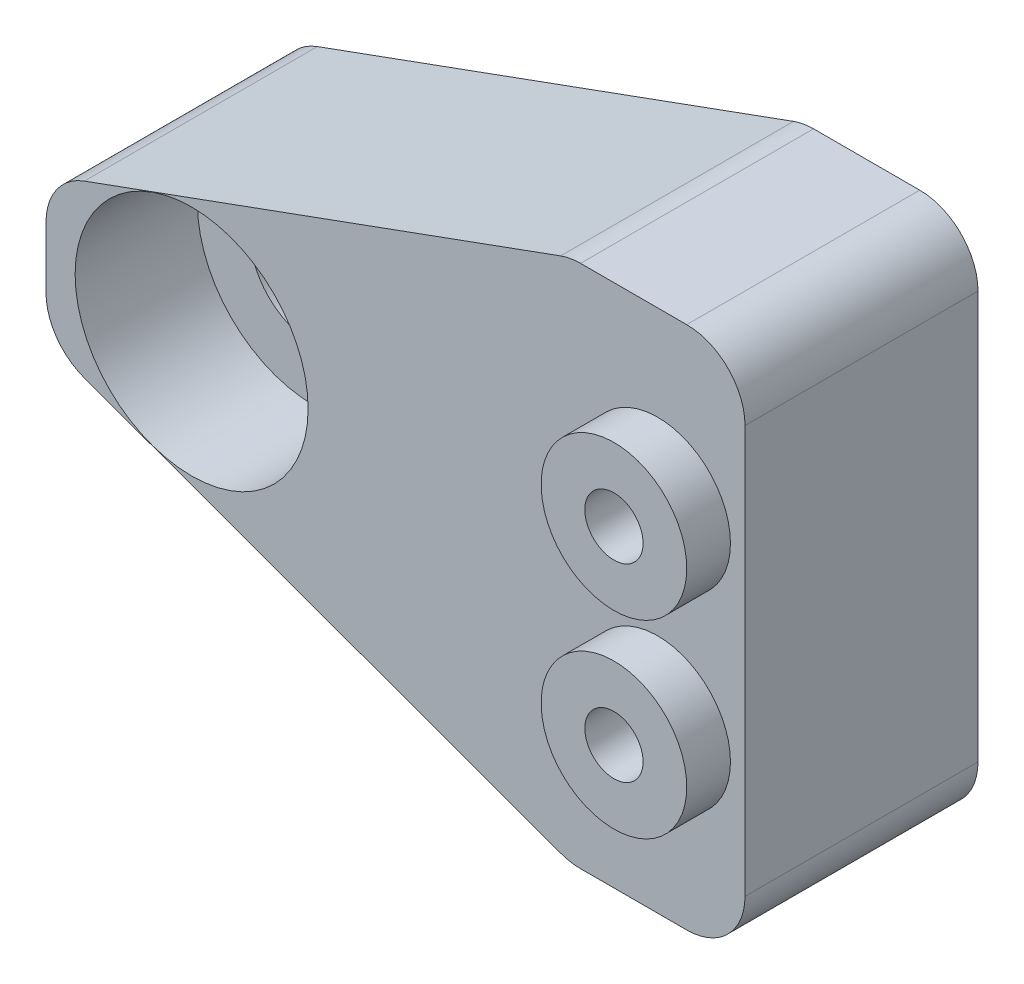
SolidWorks part; units mm, degrees
ref_plane "Plan de face" through (0, 0, 0) normal (0, 0, 1) x (1, 0, 0)
ref_plane "Plan de dessus" through (0, 0, 0) normal (0, 1, 0) x (1, 0, 0)
ref_plane "Plan de droite" through (0, 0, 0) normal (1, 0, 0) x (0, 0, -1)
sketch "Esquisse1" plane through (0, 0, 0) normal (0, 0, 1) x (1, 0, 0)
  line L1 (-8, 9) -> (16, 9)
  line L2 (-8, 9) -> (-8, -9)
  line L3 (-8, -9) -> (16, -9)
  line L4 (16, 9) -> (16, -9)
  dimension "D1" = 18
  dimension "D2" = 24
  dimension "D3" = 9
  dimension "D4" = 8
extrude "Boss.-Extru.1" add sketch "Esquisse1" along normal blind 8
sketch "Esquisse2" plane through (0, 0, 8) normal (0, 0, 1) x (1, 0, 0)
  line L0 (-8, 9) -> (-8, -9) construction
  line L1 (16, 9) -> (-8, 9) construction
  circle A0 centre (-3, 0) radius 2.2
  dimension "D1" = 4.4
  dimension "D2" = 5
  dimension "D3" = 9
extrude "Enlèv. mat.-Extru.1" cut sketch "Esquisse2" against normal through all
sketch "Esquisse3" plane through (0, 0, 8) normal (0, 0, 1) x (1, 0, 0)
  circle A0 centre (-3, 0) radius 4
  circle A1 centre (-3, 0) radius 2.2 construction
  dimension "D1" = 8
extrude "Enlèv. mat.-Extru.2" cut sketch "Esquisse3" against normal blind 4.2
sketch "Esquisse4" plane through (0, 0, 8) normal (0, 0, 1) x (1, 0, 0)
  line L0 (16, -9) -> (16, 9) construction
  circle A0 centre (13, 3.25) radius 1
  circle A1 centre (13, -3.25) radius 1
  dimension "D2" = 2
  dimension "D3" = 2
  dimension "D1" = 6.5
  dimension "D4" = 3
  dimension "D5" = 3
  dimension "D6" = 3.25
extrude "Enlèv. mat.-Extru.3" cut sketch "Esquisse4" against normal through all
sketch "Esquisse5" plane through (0, 0, 0) normal (0, 0, -1) x (-1, 0, 0)
  circle A0 centre (-13, 3.25) radius 2.6
  circle A1 centre (-13, -3.25) radius 2.6
  dimension "D1" = 5.2
  dimension "D2" = 5.2
extrude "Enlèv. mat.-Extru.6" cut sketch "Esquisse5" against normal blind 4.2
sketch "Esquisse6" plane through (0, 0, 4.2) normal (0, 0, -1) x (-1, 0, 0)
  circle A0 centre (-13, 3.25) radius 1.7
  circle A1 centre (-13, -3.25) radius 1.7
extrude "Boss.-Extru.2" add sketch "Esquisse6" against normal blind 1
chamfer "Chanfrein1" distance 18 angle 20 2 edges at (-8, -9, 4) (-8, 9, 4)
fillet "Congé1" radius 2 6 edges at (10, -9, 4) (16, -9, 4) (16, 9, 4) (10, 9, 4) (-8, -2.4485, 4) (-8, 2.4485, 4)
sketch "Esquisse7" plane through (0, 0, 8) normal (0, 0, 1) x (1, 0, 0)
  circle A0 centre (13, 3.25) radius 1
  circle A1 centre (13, -3.25) radius 1
  circle A2 centre (13, -3.25) radius 2.5
  circle A3 centre (13, 3.25) radius 2.5
  circle A4 centre (13, 3.25) radius 1 construction
  circle A5 centre (13, -3.25) radius 1 construction
  dimension "D1" = 5
  dimension "D2" = 5
extrude "Boss.-Extru.3" add sketch "Esquisse7" along normal blind 1.5
